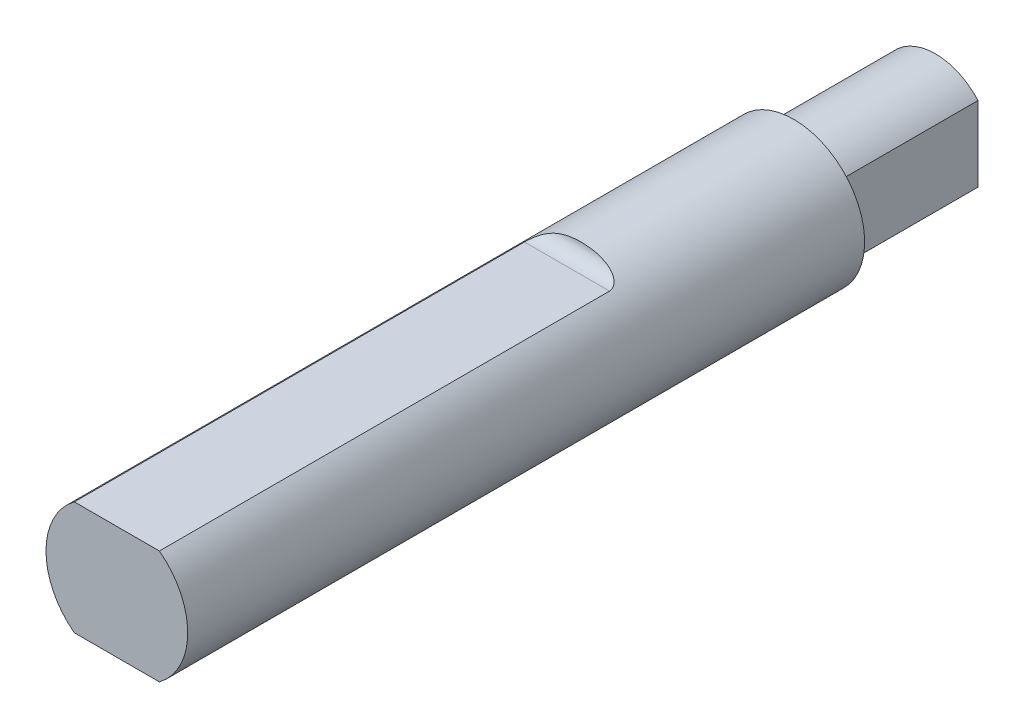
SolidWorks part; units mm, degrees
ref_plane "Front Plane" through (0, 0, 0) normal (0, 0, 1) x (1, 0, 0)
ref_plane "Top Plane" through (0, 0, 0) normal (0, 1, 0) x (1, 0, 0)
ref_plane "Right Plane" through (0, 0, 0) normal (1, 0, 0) x (0, 0, -1)
sketch "Sketch1" plane through (0, 0, 0) normal (0, 0, 1) x (1, 0, 0)
  circle A0 centre (0, 0) radius 2.5
  dimension "D1" = 5
extrude "Boss-Extrude1" add sketch "Sketch1" along normal blind 28.879
sketch "Sketch2" plane through (0, 0, 0) normal (0, 0, -1) x (-1, 0, 0)
  line L0 (-1.5, 1.3229) -> (-1.5, -1.3229)
  line L1 (1.5, -1.3229) -> (1.5, 1.3229)
  arc A1 (-1.5, -1.3229) -> (1.5, -1.3229) centre (0, 0) ccw
  arc A3 (-1.5, 1.3229) -> (1.5, 1.3229) centre (0, 0) cw
  circle A5 centre (0, 0) radius 2.5
  circle A6 centre (0, 0) radius 2.5
  dimension "D2" = 4
  dimension "D1" = 3
  dimension "D3" = 0
extrude "Cut-Extrude1" cut sketch "Sketch2" against normal blind 5
sketch "Sketch3" plane through (0, 0, 28.879) normal (0, 0, 1) x (1, 0, 0)
  line L0 (-1.5, 2) -> (1.5, 2)
  line L1 (-2.5, 0) -> (2.5, 0) construction
  line L2 (-1.5, -2) -> (1.5, -2)
  circle A0 centre (0, 0) radius 2.5 construction
  arc A1 (1.5, 2) -> (-1.5, 2) centre (0, 0) ccw
  arc A2 (1.5, -2) -> (-1.5, -2) centre (0, 0) cw
  dimension "D1" = 4
extrude "Cut-Extrude2" cut sketch "Sketch3" against normal blind 15.879
sketch "Sketch4" plane through (0, 0, 0) normal (1, 0, 0) x (0, 0, -1)
  line L0 (-13, 2.5) -> (-13, 2)
  line L1 (-12.5, 2.5) -> (-13, 2.5)
  line L2 (-13, -2.5) -> (-13, -2)
  line L3 (-13, -2) -> (-13, -2.5) construction
  line L4 (-13, -2.5) -> (-5, -2.5) construction
  line L5 (-12.5, -2.5) -> (-13, -2.5)
  line L6 (-5, 2.5) -> (-13, 2.5) construction
  arc A0 (-13, 2) -> (-12.5, 2.5) centre (-13, 2.5) ccw
  arc A1 (-13, -2) -> (-12.5, -2.5) centre (-13, -2.5) cw
extrude "Cut-Extrude3" cut sketch "Sketch4" against normal through all both and the other way through all
